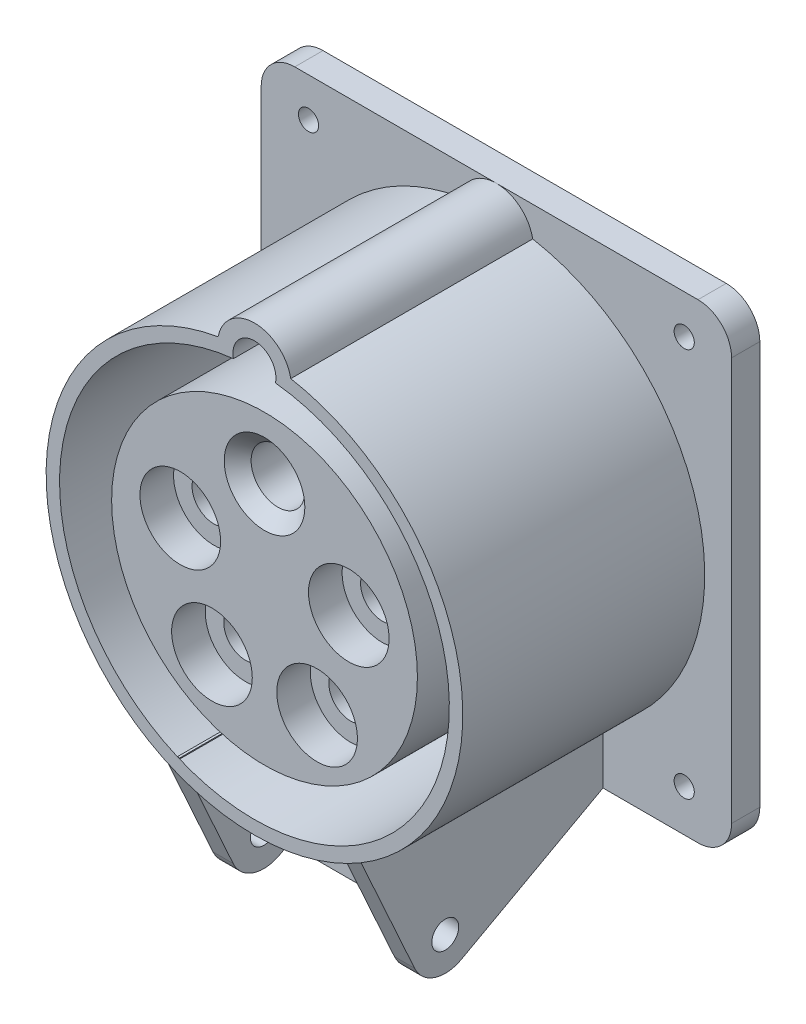
SolidWorks part; units mm, degrees
ref_plane "Front Plane" through (0, 0, 0) normal (0, 0, 1) x (1, 0, 0)
ref_plane "Top Plane" through (0, 0, 0) normal (0, 1, 0) x (1, 0, 0)
ref_plane "Right Plane" through (0, 0, 0) normal (1, 0, 0) x (0, 0, -1)
sketch "Sketch1" plane through (0, 0, 0) normal (0, 0, 1) x (1, 0, 0)
  line L0 (-264.7837, -302.4836) -> (-263.2063, -362.7236) construction
  line L5 (-0.8649, 2.2379) -> (-0.8649, -21.9058) construction
  circle A3 centre (20.9533, 12.2276) radius 4.0732
  arc A5 (17.615, -6.8714) -> (12.8025, 3.1692) centre (13.1289, -2.848) ccw
  circle A6 centre (10.8673, -18.8927) radius 3.3478
  circle A14 centre (7.8665, 14.1463) radius 6.0261
  circle A16 centre (13.1289, -2.848) radius 6.0261
  circle A18 centre (-14.8586, -2.848) radius 6.0261
  circle A22 centre (-22.683, 12.2276) radius 4.0732
  circle A25 centre (-9.5963, 14.1463) radius 6.0261
  arc A27 (-15.6157, 13.8645) -> (-7.5149, 19.8015) centre (-9.5963, 14.1463) cw
  circle A28 centre (10.8673, -18.8927) radius 2.5
  circle A29 centre (-0.8649, -14.6917) radius 7.21
  circle A30 centre (-0.8649, 2.9253) radius 22.75
  circle A31 centre (-0.8649, 2.9253) radius 25.25
  circle A32 centre (-0.8649, 2.9253) radius 27.5
  circle A33 centre (-0.8649, 2.9253) radius 30.15
  circle A34 centre (-0.8649, 2.9253) radius 28.75
  circle A35 centre (-14.8586, -2.848) radius 7.3261
  circle A36 centre (-14.8586, -2.848) radius 4.7261
  circle A37 centre (-14.8586, -2.848) radius 8.6261
  circle A41 centre (-9.5963, 14.1463) radius 7.3261
  circle A42 centre (-9.5963, 14.1463) radius 4.7261
  circle A43 centre (-9.5963, 14.1463) radius 8.6261
  circle A44 centre (13.1289, -2.848) radius 4.7261
  circle A45 centre (13.1289, -2.848) radius 7.3261
  circle A46 centre (13.1289, -2.848) radius 8.6261
  circle A47 centre (7.8665, 14.1463) radius 4.7261
  circle A48 centre (7.8665, 14.1463) radius 7.3261
  circle A49 centre (7.8665, 14.1463) radius 8.6261
  circle A50 centre (-0.8649, -14.6917) radius 8.71
  circle A51 centre (-0.8649, -14.6917) radius 6.71
  point P36 (-0.8649, 2.9253)
  point P40 (-0.8649, -26.7764)
  dimension "D1" = 5
  dimension "D2" = 14.42
  dimension "D3" = 45.5
  dimension "D4" = 50.5
  dimension "D5" = 55
  dimension "D6" = 60.3
  dimension "D7" = 57.5
  dimension "D8" = 1.3
  dimension "D9" = 1.3
  dimension "D10" = 12.0521
  dimension "D11" = 1.3
  dimension "D12" = 1.5
  dimension "D13" = 0.5
sketch "Sketch2" plane through (0, 0, 0) normal (0, 0, 1) x (1, 0, 0)
  arc A0 (-6.2684, 33.4507) -> (4.5387, 33.4507) centre (-0.8649, 2.9253) ccw
  arc A1 (4.5387, 33.4507) -> (-6.2684, 33.4507) centre (-0.8649, 32.4253) ccw
  dimension "D1" = 62
  dimension "D2" = 29.5
  dimension "D3" = 11
extrude "Boss-Extrude1" add sketch "Sketch2" along normal blind 36
sketch "Sketch3" plane through (0, 0, 36) normal (0, 0, 1) x (1, 0, 0)
  line L1 (-0.8649, 2.9253) -> (-0.8649, 50002.9253) construction
  arc A0 (-3.9941, 31.756) -> (2.2644, 31.756) centre (-0.8649, 2.9253) ccw
  arc A1 (2.2644, 31.756) -> (-3.9941, 31.756) centre (-0.8649, 32.4253) ccw
  arc A2 (-6.2684, 33.4507) -> (4.5387, 33.4507) centre (-0.8649, 2.9253) ccw construction
  circle A4 centre (-0.8649, 2.9253) radius 22.75
  dimension "D1" = 58
  dimension "D3" = 6.4
  dimension "D4" = 45.5
  dimension "D2" = 29.5
sketch "Sketch4" plane through (0, 0, 0) normal (0, 0, -1) x (-1, 0, 0)
  line L1 (-34.1351, -32.0747) -> (35.8649, -32.0747)
  line L2 (-34.1351, -32.0747) -> (-34.1351, 37.9253)
  line L3 (-34.1351, 37.9253) -> (35.8649, 37.9253)
  line L4 (35.8649, -32.0747) -> (35.8649, 37.9253)
  line L5 (-34.1351, -32.0747) -> (35.8649, 37.9253) construction
  line L6 (-34.1351, 37.9253) -> (35.8649, -32.0747) construction
  circle A0 centre (-27.0851, -25.8247) radius 1.5
  circle A1 centre (-27.0851, 32.11) radius 1.5
  circle A2 centre (28.8149, 32.11) radius 1.5
  circle A3 centre (28.8149, -25.8247) radius 1.5
  point P0 (0.8649, 2.9253)
  dimension "D1" = 70
extrude "Boss-Extrude2" add sketch "Sketch4" along normal blind 4.2
fillet "Fillet1" radius 5 4 edges at (-35.8649, 37.9253, -2.1) (-35.8649, -32.0747, -2.1) (34.1351, -32.0747, -2.1) (34.1351, 37.9253, -2.1)
extrude "Cut-Extrude1" cut sketch "Sketch3" against normal blind 38.5
sketch "Sketch7" plane through (0, 0, 36) normal (0, 0, 1) x (1, 0, 0)
  circle A0 centre (-0.8649, 2.9253) radius 22.75
  circle A1 centre (-0.8649, 2.9253) radius 22.75 construction
extrude "Cut-Extrude2" cut sketch "Sketch7" against normal blind 1.5 contours A0
sketch "Sketch8" plane through (0, 0, 34.5) normal (0, 0, 1) x (1, 0, 0)
  line L0 (246.2964, 307.8954) -> (244.7189, 368.1354) construction
  line L5 (-0.8649, 3.6126) -> (-0.8649, 27.7563) construction
  circle A3 centre (-22.683, -6.3771) radius 4.0732
  arc A5 (-19.3448, 12.722) -> (-14.5323, 2.6814) centre (-14.8586, 8.6986) ccw
  circle A6 centre (-12.597, 24.7432) radius 3.3478
  circle A14 centre (-9.5963, -8.2957) radius 6.0261
  circle A16 centre (-14.8586, 8.6986) radius 6.0261
  circle A18 centre (13.1289, 8.6986) radius 6.0261
  circle A22 centre (20.9533, -6.3771) radius 4.0732
  circle A25 centre (7.8665, -8.2957) radius 6.0261
  arc A27 (13.886, -8.014) -> (5.7852, -13.9509) centre (7.8665, -8.2957) cw
  circle A28 centre (-12.597, 24.7432) radius 2.5
  circle A29 centre (-0.8649, 20.5423) radius 7.21
  circle A30 centre (-0.8649, 2.9253) radius 22.75
  circle A31 centre (-0.8649, 2.9253) radius 25.25
  circle A32 centre (-0.8649, 2.9253) radius 27.5
  circle A33 centre (-0.8649, 2.9253) radius 30.15
  circle A34 centre (-0.8649, 2.9253) radius 28.75
  circle A35 centre (13.1289, 8.6986) radius 7.3261
  circle A36 centre (13.1289, 8.6986) radius 4.7261
  circle A37 centre (13.1289, 8.6986) radius 8.6261
  circle A41 centre (7.8665, -8.2957) radius 7.3261
  circle A42 centre (7.8665, -8.2957) radius 4.7261
  circle A43 centre (7.8665, -8.2957) radius 8.6261
  circle A44 centre (-14.8586, 8.6986) radius 4.7261
  circle A45 centre (-14.8586, 8.6986) radius 7.3261
  circle A46 centre (-14.8586, 8.6986) radius 8.6261
  circle A47 centre (-9.5963, -8.2957) radius 4.7261
  circle A48 centre (-9.5963, -8.2957) radius 7.3261
  circle A49 centre (-9.5963, -8.2957) radius 8.6261
  circle A50 centre (-0.8649, 20.5423) radius 8.71
  circle A51 centre (-0.8649, 20.5423) radius 6.71
  point P36 (-0.8649, 2.9253)
  point P40 (-0.8649, 32.627)
  dimension "D1" = 5
  dimension "D2" = 14.42
  dimension "D3" = 45.5
  dimension "D4" = 50.5
  dimension "D5" = 55
  dimension "D6" = 60.3
  dimension "D7" = 57.5
  dimension "D8" = 1.3
  dimension "D9" = 1.3
  dimension "D10" = 12.0521
  dimension "D11" = 1.3
  dimension "D12" = 1.5
  dimension "D13" = 0.5
sketch "Sketch9" plane through (0, 0, 34.5) normal (0, 0, 1) x (1, 0, 0)
  line L0 (-236.4959, -273.0632) -> (-235.0824, -327.0447) construction
  line L9 (-0.8649, 2.6442) -> (-0.8649, 50002.6442) construction
  line L18 (29.1351, -32.0747) -> (-30.8649, -32.0747) construction
  arc A2 (4.5387, 33.4507) -> (-6.2684, 33.4507) centre (-0.8649, 32.4253) ccw construction
  arc A6 (-9.4708, 10.2893) -> (-8.1774, 2.8106) centre (-13.4036, 5.7579) ccw
  circle A8 centre (-0.8649, 16.4253) radius 4
  circle A15 centre (-8.6855, -9.4681) radius 6
  circle A17 centre (-13.4036, 5.7579) radius 6
  circle A19 centre (11.6738, 5.7579) radius 6
  circle A26 centre (6.9558, -9.4681) radius 6
  point P12 (-0.8649, 37.9253)
  point P39 (-0.8649, 2.0283)
  point P43 (-0.8649, 28.6442)
  dimension "D2" = 25.0774
  dimension "D3" = 15.6413
  dimension "D5" = 12
  dimension "D6" = 25.8934
  dimension "D7" = 21.5
  dimension "D11" = 8
  dimension "D9" = 12
  dimension "D1" = 54
  dimension "D4" = 10.6674
extrude "Cut-Extrude3" cut sketch "Sketch9" against normal blind 5 contours A17 | A19 | A26 | A15
sketch "Sketch11" plane through (0, 0, 29.5) normal (0, 0, 1) x (1, 0, 0)
  circle A0 centre (11.6738, 5.7579) radius 3.25
  circle A1 centre (-13.4036, 5.7579) radius 3.25
  circle A2 centre (-8.6855, -9.4681) radius 3.25
  circle A3 centre (6.9558, -9.4681) radius 3.25
  circle A4 centre (11.6738, 5.7579) radius 6 construction
  circle A5 centre (-13.4036, 5.7579) radius 6 construction
  circle A6 centre (-8.6855, -9.4681) radius 6 construction
  circle A7 centre (6.9558, -9.4681) radius 6 construction
  dimension "D1" = 6.5
extrude "Cut-Extrude4" cut sketch "Sketch11" against normal blind 12
sketch "Sketch12" plane through (0, 0, 17.5) normal (0, 0, 1) x (1, 0, 0)
  circle A0 centre (11.6738, 5.7579) radius 4
  circle A1 centre (6.9558, -9.4681) radius 4
  circle A2 centre (-8.6855, -9.4681) radius 4
  circle A3 centre (-13.4036, 5.7579) radius 4
  circle A4 centre (-13.4036, 5.7579) radius 3.25 construction
  circle A5 centre (-8.6855, -9.4681) radius 3.25 construction
  circle A6 centre (6.9558, -9.4681) radius 3.25 construction
  circle A7 centre (11.6738, 5.7579) radius 3.25 construction
  dimension "D1" = 8
extrude "Cut-Extrude5" cut sketch "Sketch12" against normal through all contours A0 | A1 | A2 | A3
sketch "Sketch14" plane through (0, 0, 34.5) normal (0, 0, 1) x (1, 0, 0)
  line L0 (-0.8649, 17.6361) -> (-0.8649, 50017.6361) construction
  arc A0 (-9.4708, 10.2893) -> (-8.1774, 2.8106) centre (-13.4036, 5.7579) ccw
  circle A1 centre (-0.8649, 16.4253) radius 4
  circle A2 centre (-8.6855, -9.4681) radius 6
  circle A3 centre (-13.4036, 5.7579) radius 6
  circle A4 centre (11.6738, 5.7579) radius 6
  circle A5 centre (6.9558, -9.4681) radius 6
  circle A6 centre (11.6738, 5.7579) radius 6 construction
  point P10 (-0.8649, 17.0202)
  point P11 (-0.8649, 43.6361)
  dimension "D1" = 8
  dimension "D2" = 12
  dimension "D3" = 12
  dimension "D4" = 25.0774
  dimension "D5" = 15.6413
  dimension "D6" = 10.6674
  dimension "D7" = 25.8934
extrude "Cut-Extrude6" cut sketch "Sketch14" against normal blind 8 contours A1
chamfer "Chamfer1" distance 2 angle 45 1 edges at (3.1351, 16.4253, 34.5)
sketch "Sketch15" plane through (0, 0, 26.5) normal (0, 0, 1) x (1, 0, 0)
  circle A0 centre (-0.8649, 16.4253) radius 5
  circle A1 centre (-0.8649, 16.4253) radius 4 construction
  dimension "D1" = 10
extrude "Cut-Extrude7" cut sketch "Sketch15" against normal through all
sketch "Sketch16" plane through (0, 0, -4.2) normal (0, 0, -1) x (-1, 0, 0)
  line L0 (0.8649, 37.9253) -> (0.8649, -32.0747) construction
  line L1 (30.8649, 37.9253) -> (-29.1351, 37.9253) construction
  line L2 (-29.1351, -32.0747) -> (30.8649, -32.0747) construction
  line L3 (-34.1351, 2.9253) -> (35.8649, 2.9253) construction
  line L4 (-34.1351, 32.9253) -> (-34.1351, -27.0747) construction
  line L5 (35.8649, -27.0747) -> (35.8649, 32.9253) construction
  circle A0 centre (0.8649, 2.9253) radius 27.5
  circle A1 centre (0.8649, 2.9253) radius 25.2
  dimension "D1" = 55
  dimension "D2" = 50.4
extrude "Boss-Extrude3" add sketch "Sketch16" along normal blind 2.7 contours A0 | A1
ref_plane "Plane1" through (15, 0, 0) normal (1, 0, 0) x (0, 0, -1)
sketch "Sketch17" plane through (15, 0, 0) normal (1, 0, 0) x (0, 0, -1)
  line L0 (0, 33.4507) -> (0, -28.0747) construction
  line L4 (-36, 33.4507) -> (-36, -28.0747) construction
  line L5 (-36, 33.4507) -> (-36, -39.6507) construction
  line L6 (0, 33.4507) -> (0, -39.6507) construction
  line L11 (0, -23.7075) -> (-36, -23.7075)
  line L12 (-36, 29.5581) -> (0, 29.5581)
  line L13 (-36, 29.5581) -> (0, 29.5581)
  line L14 (0, -23.7075) -> (-36, -23.7075)
  line L15 (0, 37.9253) -> (0, 29.5581)
  line L16 (0, -23.7075) -> (0, -32.0747)
  line L17 (0, -23.7075) -> (0, -32.0747)
  line L18 (0, 37.9253) -> (0, 29.5581)
  line L19 (-36, -23.7075) -> (0, -23.7075)
  line L20 (-36, -23.7075) -> (-25.8, -46.2075)
  line L21 (0, -23.7075) -> (0, -32.0747)
  line L22 (-25.8, -46.2075) -> (0, -32.0747)
  circle A0 centre (-23.4726, -39.2316) radius 2
  dimension "D5" = 4
  dimension "D1" = 30
  dimension "D2" = 22.5
  dimension "D3" = 5
  dimension "D4" = 5
extrude "Boss-Extrude4" add sketch "Sketch17" against normal blind 3 contours L20 L22 L17 L14 A0
mirror "Mirror1" about plane through (0, 0, 0) normal (1, 0, 0) of "Boss-Extrude4"
sketch "Sketch19" plane through (0, 0, 0) normal (1, 0, 0) x (0, 0, -1)
  line L0 (0, 32.9253) -> (0, -27.0747) construction
  line L1 (0, 32.9253) -> (0, -27.0747) construction
  line L2 (-34.9581, -26.0058) -> (0, -26.0058) construction
  line L3 (0, -25.2792) -> (0, -28.0747) construction
  line L4 (0, -25.2792) -> (-35.2875, -25.2792) construction
  line L5 (-36, -23.7075) -> (-35.2875, -25.2792) construction
  line L6 (-35.2875, -25.2792) -> (-25.8, -46.2075)
  line L7 (0, -25.2792) -> (-35.2875, -25.2792)
  line L8 (0, -32.0747) -> (0, -25.2792)
  line L9 (-25.8, -46.2075) -> (0, -32.0747)
  line L10 (-35.2875, -25.2792) -> (-25.8, -46.2075) construction
  line L11 (0, -25.2792) -> (-35.2875, -25.2792) construction
  line L12 (0, -32.0747) -> (0, -25.2792) construction
  line L13 (-25.8, -46.2075) -> (0, -32.0747) construction
  line L14 (-36, 33.4507) -> (-36, -28.0747) construction
  line L15 (-36, 33.4507) -> (0, 33.4507) construction
  line L16 (0, 33.4507) -> (0, -24.6645) construction
  line L18 (-35.5662, -24.6645) -> (-34.9581, -26.0058) construction
  line L19 (-36, 33.4507) -> (-36, -23.7075) construction
  line L21 (0, 33.4507) -> (0, -23.7075) construction
  line L22 (0, 33.4507) -> (-36, 33.4507) construction
  line L23 (-36, 33.4507) -> (-36, -23.7075) construction
  line L24 (0, -26.0058) -> (0, -32.0747)
  line L25 (0, 33.4507) -> (0, -23.7075) construction
  line L26 (0, 33.4507) -> (-36, 33.4507)
  line L27 (-34.9581, -26.0058) -> (0, -26.0058) construction
  line L28 (0, -25.2792) -> (0, -28.0747) construction
  line L29 (0, -25.2792) -> (-35.2875, -25.2792) construction
  line L30 (-36, -23.7075) -> (-35.2875, -25.2792) construction
  line L31 (-36, 33.4507) -> (-36, -28.0747) construction
  line L32 (-36, 33.4507) -> (0, 33.4507)
  line L33 (0, 33.4507) -> (0, -24.6645)
  line L34 (0, -26.0058) -> (-18, -26.0058)
  line L35 (-35.5662, -24.6645) -> (-34.9581, -26.0058) construction
  line L36 (0, -32.0747) -> (-18, -41.9348)
  line L37 (-18, -26.0058) -> (-18, -41.9348)
  dimension "D2" = 18
  dimension "D1" = 0
extrude "Boss-Extrude5" add sketch "Sketch19" along normal blind 0.8 and the other way blind 0.8 contours L24 L34 L37 L36
sketch "Sketch20" plane through (0, -24.6716, -13.5147) normal (0, -0.877, -0.4804) x (1, 0, 0)
  line L0 (-0.8, 35.9332) -> (0.8, 35.9332) construction
  line L1 (12, 44.8268) -> (12, 15.4095) construction
  line L2 (-12, 44.8268) -> (-12, 15.4095) construction
  line L3 (-0.8, 35.9332) -> (0.8, 35.9332) construction
  line L4 (12, 44.8268) -> (12, 15.4095) construction
  line L5 (-12, 44.8268) -> (-12, 15.4095) construction
  line L6 (-12, 15.4095) -> (12, 15.4095)
  line L7 (-12, 15.4095) -> (-12, 37.9332)
  line L8 (12, 15.4095) -> (12, 37.9332)
  line L9 (-12, 37.9332) -> (12, 37.9332)
  line L10 (29.1351, 15.4095) -> (15, 15.4095)
  line L11 (15, 15.4095) -> (12, 15.4095)
  line L12 (12, 15.4095) -> (0.8, 15.4095)
  line L13 (0.8, 15.4095) -> (-0.8, 15.4095)
  line L14 (-0.8, 15.4095) -> (-12, 15.4095)
  line L15 (-12, 15.4095) -> (-15, 15.4095)
  line L16 (-15, 15.4095) -> (-30.8649, 15.4095)
  line L17 (-30.8649, 15.4095) -> (-30.8649, 11.726)
  line L18 (-30.8649, 11.726) -> (29.1351, 11.726)
  line L19 (29.1351, 11.726) -> (29.1351, 15.4095)
  line L20 (29.1351, 15.4095) -> (15, 15.4095) construction
  line L21 (15, 15.4095) -> (12, 15.4095) construction
  line L22 (12, 15.4095) -> (0.8, 15.4095) construction
  line L23 (0.8, 15.4095) -> (-0.8, 15.4095) construction
  line L24 (-0.8, 15.4095) -> (-12, 15.4095) construction
  line L25 (-12, 15.4095) -> (-15, 15.4095) construction
  line L26 (-15, 15.4095) -> (-30.8649, 15.4095) construction
  line L27 (-30.8649, 15.4095) -> (-30.8649, 11.726) construction
  line L28 (-30.8649, 11.726) -> (29.1351, 11.726) construction
  line L29 (29.1351, 11.726) -> (29.1351, 15.4095) construction
  dimension "D2" = 2
  dimension "D1" = 0
extrude "Boss-Extrude6" add sketch "Sketch20" along direction (0, -1, 0) on the side against the normal blind 2 contours L6 L7 L9 L8
fillet "Fillet2" radius 5 2 edges at (-13.5, -46.2075, 25.8) (13.5, -46.2075, 25.8)
sketch "Sketch22" plane through (0, 0, 36) normal (0, 0, 1) x (1, 0, 0)
  arc A3 (4.5387, 33.4507) -> (-6.2684, 33.4507) centre (-0.8649, 32.4253) ccw
  arc A4 (-6.2684, 33.4507) -> (15, -23.7075) centre (-0.8649, 2.9253) ccw
  arc A5 (15, -23.7075) -> (4.5387, 33.4507) centre (-0.8649, 2.9253) ccw
  arc A6 (4.5387, 33.4507) -> (-6.2684, 33.4507) centre (-0.8649, 32.4253) ccw
  arc A7 (-6.2684, 33.4507) -> (15, -23.7075) centre (-0.8649, 2.9253) ccw
  arc A8 (15, -23.7075) -> (4.5387, 33.4507) centre (-0.8649, 2.9253) ccw
  dimension "D1" = 0
ref_plane "Plane2" through (12, -40.8957, 19.7541) normal (1, 0, 0) x (0, 0, -1)
sketch "Sketch23" plane through (0, 0, 0) normal (1, 0, 0) x (0, 0, -1)
  line L6 (-34.9581, -26.0058) -> (-28.0265, -41.296)
  line L7 (-21.0705, -43.6168) -> (-19.7541, -42.8957)
  line L8 (-19.7541, -42.8957) -> (-19.7541, -40.8957)
  line L9 (-19.7541, -40.8957) -> (0, -30.0747)
  line L10 (0, -30.0747) -> (0, -26.0058)
  line L11 (0, -26.0058) -> (-34.9581, -26.0058)
  line L12 (-34.9581, -26.0058) -> (-28.0265, -41.296) construction
  line L13 (-21.0705, -43.6168) -> (-19.7541, -42.8957) construction
  line L14 (-19.7541, -42.8957) -> (-19.7541, -40.8957) construction
  line L15 (-19.7541, -40.8957) -> (0, -30.0747) construction
  line L16 (0, -30.0747) -> (0, -26.0058) construction
  line L17 (0, -26.0058) -> (-34.9581, -26.0058) construction
  circle A0 centre (-23.4726, -39.2316) radius 2 construction
  arc A1 (-28.0265, -41.296) -> (-21.0705, -43.6168) centre (-23.4726, -39.2316) ccw
  arc A2 (-28.0265, -41.296) -> (-21.0705, -43.6168) centre (-23.4726, -39.2316) ccw construction
  circle A3 centre (-23.4726, -39.2316) radius 2 construction
  dimension "D1" = 0
